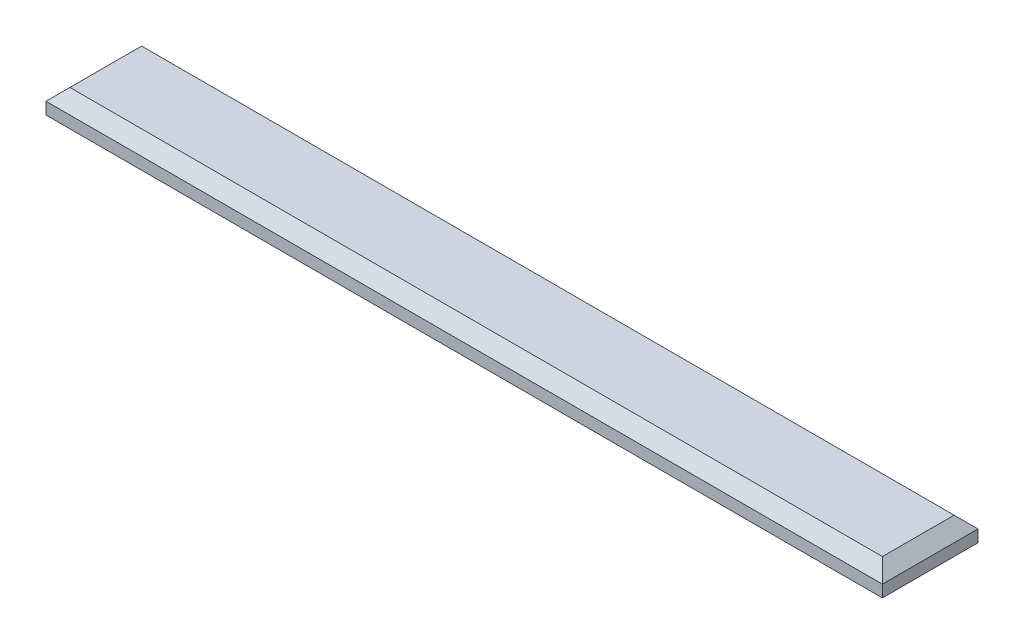
SolidWorks part; units mm, degrees
ref_plane "Front Plane" through (0, 0, 0) normal (0, 0, 1) x (1, 0, 0)
ref_plane "Top Plane" through (0, 0, 0) normal (0, 1, 0) x (1, 0, 0)
ref_plane "Right Plane" through (0, 0, 0) normal (1, 0, 0) x (0, 0, -1)
sketch "Sketch1" plane through (0, 0, 0) normal (0, 1, 0) x (1, 0, 0)
  line L1 (0, 0) -> (70, 0)
  line L2 (0, 0) -> (0, 8)
  line L3 (0, 8) -> (70, 8)
  line L4 (70, 0) -> (70, 8)
  dimension "D1" = 70
  dimension "D2" = 8
extrude "Boss-Extrude1" add sketch "Sketch1" along normal blind 2
chamfer "Chamfer1" distance 1 angle 45 4 edges at (35, 2, -8) (70, 2, -4) (35, 2, 0) (0, 2, -4)
